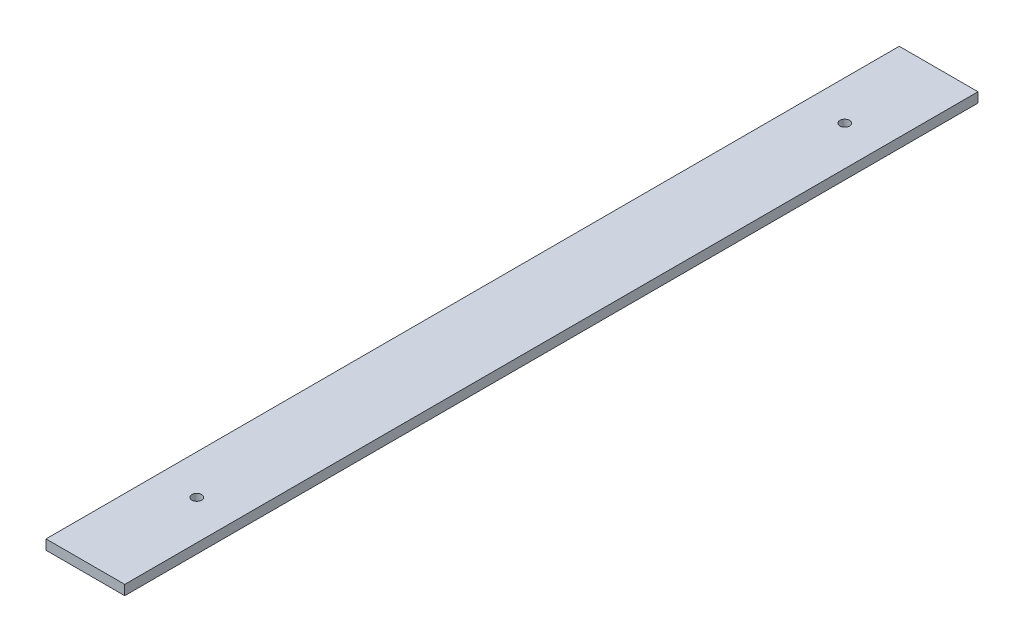
SolidWorks part; units mm, degrees
material "6063-O"
ref_plane "Front Plane" through (0, 0, 0) normal (0, 0, 1) x (1, 0, 0)
ref_plane "Top Plane" through (0, 0, 0) normal (0, 1, 0) x (1, 0, 0)
ref_plane "Right Plane" through (0, 0, 0) normal (1, 0, 0) x (0, 0, -1)
sketch "Sketch4" plane through (0, 0, 0) normal (0, 1, 0) x (1, 0, 0)
  line L4 (23232.9446, -10111.0305) -> (23232.9446, -10251.0305) construction
  line L5 (23232.9446, -9942.5829) -> (23032.9446, -9942.5829)
  line L6 (23232.9446, -9942.5829) -> (23232.9446, -12876.1567)
  line L7 (23232.9446, -12876.1567) -> (23032.9446, -12876.1567)
  line L8 (23032.9446, -9942.5829) -> (23032.9446, -12876.1567)
  line L9 (22132.9446, -9942.5829) -> (21932.9446, -9942.5829)
  line L10 (22132.9446, -9942.5829) -> (22132.9446, -12833.5838)
  line L11 (22132.9446, -12833.5838) -> (21932.9446, -12833.5838)
  line L12 (21932.9446, -9942.5829) -> (21932.9446, -12833.5838)
  line L13 (20932.9446, -9942.5829) -> (20732.9446, -9942.5829)
  line L14 (20932.9446, -9942.5829) -> (20932.9446, -12599.4325)
  line L15 (20932.9446, -12599.4325) -> (20732.9446, -12599.4325)
  line L16 (20732.9446, -9942.5829) -> (20732.9446, -12599.4325)
  line L17 (19732.9446, -9942.5829) -> (19532.9446, -9942.5829)
  line L18 (19732.9446, -9942.5829) -> (19732.9446, -12109.8436)
  line L19 (19732.9446, -12109.8436) -> (19532.9446, -12109.8436)
  line L20 (19532.9446, -9942.5829) -> (19532.9446, -12109.8436)
  line L21 (18902.9446, -9942.5829) -> (18702.9446, -9942.5829)
  line L22 (18902.9446, -9942.5829) -> (18902.9446, -11636.2195)
  line L23 (18902.9446, -11636.2195) -> (18702.9446, -11636.2195)
  line L24 (18702.9446, -9942.5829) -> (18702.9446, -11636.2195)
  line L25 (18702.9446, -10111.0305) -> (18702.9446, -10251.0305) construction
  line L26 (23132.9446, -12748.1199) -> (23132.9446, -12608.0593) construction
  line L27 (22032.9446, -12550.6075) -> (22032.9446, -12691.8491) construction
  line L28 (20832.9446, -12422.3488) -> (20832.9446, -12275.1597) construction
  line L29 (19632.9446, -11906.9658) -> (19632.9446, -11746.8651) construction
  line L30 (18802.9446, -11371.765) -> (18802.9446, -11195.5746) construction
  line L31 (23132.9446, -10251.0305) -> (23132.9446, -10111.0305) construction
  line L32 (18702.9446, -10251.0305) -> (23232.9446, -10251.0305) construction
  line L33 (23232.9446, -10111.0305) -> (18702.9446, -10111.0305) construction
  circle A0 centre (23132.9446, -12678.0896) radius 12.5
  arc A1 (18702.9446, -11295.1434) -> (23232.9446, -12744.4799) centre (22932.9446, -5878.0705) ccw construction
  arc A2 (18702.9446, -11116.3765) -> (23232.9446, -12604.3436) centre (22932.9446, -5878.0705) ccw construction
  circle A3 centre (22032.9446, -12621.2283) radius 12.5
  circle A4 centre (20832.9446, -12348.7542) radius 12.5
  circle A5 centre (19632.9446, -11826.9154) radius 12.5
  circle A6 centre (18802.9446, -11283.6698) radius 12.5
  circle A7 centre (18802.9446, -10181.0305) radius 12.5
  circle A8 centre (19632.9446, -10181.0305) radius 12.5
  circle A9 centre (20832.9446, -10181.0305) radius 12.5
  circle A10 centre (22032.9446, -10181.0305) radius 12.5
  circle A11 centre (23132.9446, -10181.0305) radius 12.5
  arc A12 (18702.9446, -11116.3765) -> (23232.9446, -12604.3436) centre (22932.9446, -5878.0705) ccw construction
  point P22 (23132.9446, -9942.5829)
  point P23 (22032.9446, -9942.5829)
  point P24 (20832.9446, -9942.5829)
  point P25 (19632.9446, -9942.5829)
  point P26 (23132.9446, -12876.1567)
  point P30 (20832.9446, -12599.4325)
  point P40 (23132.9446, -12678.0896)
  point P59 (22032.9446, -12621.2283)
  point P60 (22032.9446, -12833.5838)
  point P68 (20832.9446, -12348.7542)
  point P69 (19632.9446, -12109.8436)
  point P73 (19632.9446, -11826.9154)
  point P74 (18802.9446, -11283.6698)
  point P75 (18802.9446, -11636.2195)
  point P78 (23132.9446, -10181.0305)
  point P91 (18802.9446, -9942.5829)
  dimension "D5" = 25
  dimension "D1" = 200
  dimension "D2" = 1200
  dimension "D3" = 1200
  dimension "D4" = 1200
  dimension "D6" = 100
  dimension "D7" = 70
extrude "Boss-Extrude1" add sketch "Sketch4" along normal blind 25
sketch "Sketch5" plane through (0, 0, 0) normal (0, 1, 0) x (1, 0, 0)
  line L1 (19134.9317, -13286.4455) -> (17795.4223, -13286.4455)
  line L2 (19134.9317, -13286.4455) -> (19134.9317, -8351.4107)
  line L3 (19134.9317, -8351.4107) -> (17795.4223, -8351.4107)
  line L4 (17795.4223, -13286.4455) -> (17795.4223, -8351.4107)
  line L5 (20227.6894, -13868.0747) -> (20721.1929, -13868.0747)
  line L6 (20227.6894, -13868.0747) -> (20227.6894, -12986.8184)
  line L7 (20227.6894, -12986.8184) -> (20721.1929, -12986.8184)
  line L8 (20721.1929, -13868.0747) -> (20721.1929, -12986.8184)
  line L9 (24898.3474, -7487.7797) -> (20051.4382, -7487.7797)
  line L10 (24898.3474, -7487.7797) -> (24898.3474, -14502.5791)
  line L11 (24898.3474, -14502.5791) -> (20051.4382, -14502.5791)
  line L12 (20051.4382, -7487.7797) -> (20051.4382, -14502.5791)
extrude "Cut-Extrude1" cut sketch "Sketch5" along normal through all
